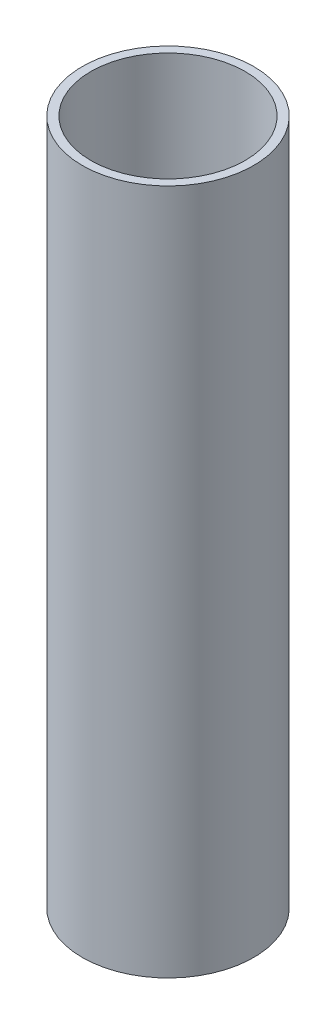
SolidWorks part; units mm, degrees
ref_plane "Front Plane" through (0, 0, 0) normal (0, 0, 1) x (1, 0, 0)
ref_plane "Top Plane" through (0, 0, 0) normal (0, 1, 0) x (1, 0, 0)
ref_plane "Right Plane" through (0, 0, 0) normal (1, 0, 0) x (0, 0, -1)
sketch "Sketch1" plane through (0, 0, 0) normal (0, 1, 0) x (1, 0, 0)
  circle A0 centre (0, 0) radius 22.5
  circle A1 centre (0, 0) radius 25
  dimension "D1" = 45
  dimension "D2" = 50
extrude "Boss-Extrude1" add sketch "Sketch1" along normal blind 200
